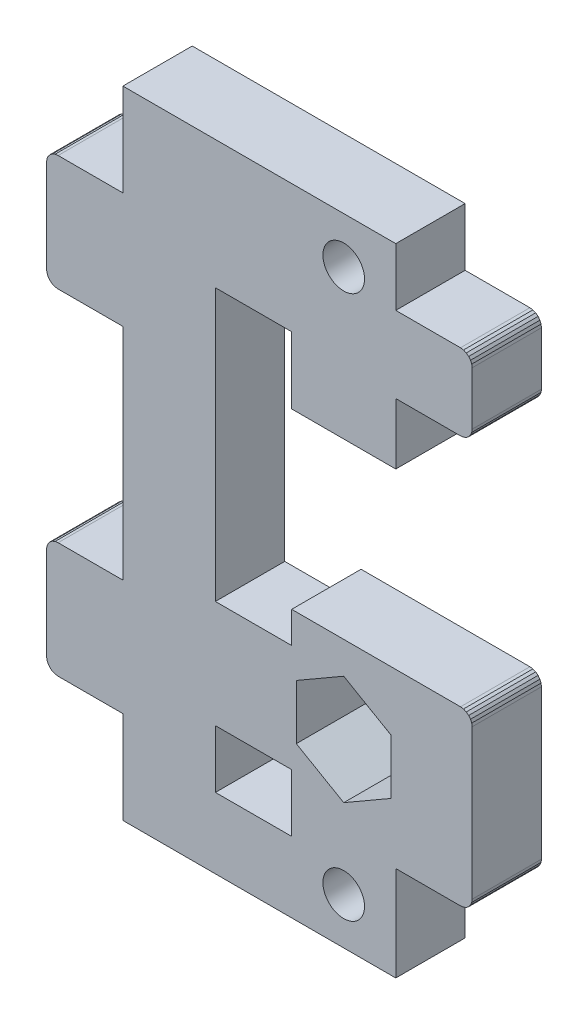
SolidWorks part; units mm, degrees
ref_plane "Plano frontal" through (0, 0, 0) normal (0, 0, 1) x (1, 0, 0)
ref_plane "Plano superior" through (0, 0, 0) normal (0, 1, 0) x (1, 0, 0)
ref_plane "Plano direito" through (0, 0, 0) normal (1, 0, 0) x (0, 0, -1)
sketch "Model" plane through (0, 0, 0) normal (0, 0, 1) x (1, 0, 0)
  line L0 (65.7238, 35.0744) -> (65.6239, 35.3156)
  line L1 (65.6239, 35.3156) -> (65.4649, 35.5227)
  line L2 (65.7578, 34.8156) -> (65.7238, 35.0744)
  line L3 (65.4649, 35.5227) -> (65.2578, 35.6816)
  line L4 (29.4578, 30.5694) -> (29.2507, 30.4104)
  line L5 (29.0918, 30.2033) -> (28.9919, 29.9621)
  line L6 (29.9578, 59.7033) -> (29.699, 59.6693)
  line L7 (29.9578, 20.7033) -> (35.5578, 20.7033)
  line L8 (29.9578, 20.7033) -> (29.699, 20.7374)
  line L9 (65.2578, 62.5694) -> (65.4649, 62.4104)
  line L10 (59.1578, 12.7033) -> (35.5578, 12.7033)
  line L11 (64.7578, 35.8156) -> (50.1578, 35.8156)
  line L12 (28.9919, 29.9621) -> (28.9578, 29.7033)
  line L13 (65.7238, 56.8445) -> (65.7578, 57.1033)
  line L14 (43.5578, 23.8033) -> (43.5618, 18.8033)
  line L15 (50.1578, 56.6033) -> (50.1578, 50.8208)
  line L16 (29.9578, 59.7033) -> (35.5578, 59.7033)
  line L17 (29.699, 30.6693) -> (29.4578, 30.5694)
  line L18 (28.9919, 21.4445) -> (28.9578, 21.7033)
  line L19 (65.0166, 62.6693) -> (65.2578, 62.5694)
  line L20 (29.4578, 59.5694) -> (29.2507, 59.4104)
  line L21 (29.4578, 49.8373) -> (29.699, 49.7374)
  line L22 (35.5578, 49.7033) -> (35.5578, 30.7033)
  line L23 (43.5578, 33.1033) -> (43.5578, 56.6033)
  line L24 (29.699, 59.6693) -> (29.4578, 59.5694)
  line L25 (28.9578, 21.7033) -> (28.9578, 29.7033)
  line L26 (64.7578, 56.1033) -> (65.0166, 56.1374)
  line L27 (65.6239, 62.2033) -> (65.7238, 61.9621)
  line L28 (65.4649, 21.1962) -> (65.6239, 21.4033)
  line L29 (29.2507, 49.9962) -> (29.4578, 49.8373)
  line L30 (65.0166, 35.7815) -> (64.7578, 35.8156)
  line L31 (65.4649, 62.4104) -> (65.6239, 62.2033)
  line L32 (64.7578, 62.7033) -> (59.1578, 62.7033)
  line L33 (65.7238, 21.6445) -> (65.7578, 21.9033)
  line L34 (29.9578, 49.7033) -> (35.5578, 49.7033)
  line L35 (59.1578, 20.9033) -> (59.1578, 12.7033)
  line L36 (28.9578, 50.7033) -> (28.9578, 58.7033)
  line L37 (65.6239, 56.6033) -> (65.7238, 56.8445)
  line L38 (65.4649, 56.3962) -> (65.6239, 56.6033)
  line L39 (29.0918, 50.2033) -> (29.2507, 49.9962)
  line L40 (65.2578, 21.0373) -> (65.4649, 21.1962)
  line L41 (35.5578, 67.7033) -> (35.5578, 59.7033)
  line L42 (28.9578, 50.7033) -> (28.9919, 50.4445)
  line L43 (29.699, 20.7374) -> (29.4578, 20.8373)
  line L44 (50.1578, 23.8085) -> (43.5578, 23.8033)
  line L45 (65.2578, 35.6816) -> (65.0166, 35.7815)
  line L46 (29.9578, 30.7033) -> (29.699, 30.6693)
  line L47 (59.1578, 20.9033) -> (64.7578, 20.9033)
  line L48 (65.7578, 34.8156) -> (65.7578, 21.9033)
  line L49 (65.6239, 21.4033) -> (65.7238, 21.6445)
  line L50 (65.2578, 56.2373) -> (65.4649, 56.3962)
  line L51 (35.5578, 67.7033) -> (59.1578, 67.7033)
  line L52 (65.0166, 56.1374) -> (65.2578, 56.2373)
  line L53 (43.5578, 56.6033) -> (50.1578, 56.6033)
  line L54 (29.2507, 20.9962) -> (29.0918, 21.2033)
  line L55 (29.699, 49.7374) -> (29.9578, 49.7033)
  line L56 (59.1578, 56.1033) -> (59.1578, 50.8208)
  line L57 (28.9919, 58.9621) -> (28.9578, 58.7033)
  line L58 (43.5618, 18.8033) -> (50.1618, 18.8085)
  line L59 (29.0918, 21.2033) -> (28.9919, 21.4445)
  line L60 (29.2507, 59.4104) -> (29.0918, 59.2033)
  line L61 (29.0918, 59.2033) -> (28.9919, 58.9621)
  line L62 (29.2507, 30.4104) -> (29.0918, 30.2033)
  line L63 (35.5578, 30.7033) -> (29.9578, 30.7033)
  line L64 (50.1578, 33.1033) -> (43.5578, 33.1033)
  line L65 (64.7578, 20.9033) -> (65.0166, 20.9374)
  line L66 (59.1578, 62.7033) -> (59.1578, 67.7033)
  line L67 (65.0166, 20.9374) -> (65.2578, 21.0373)
  line L68 (50.1618, 18.8085) -> (50.1578, 23.8085)
  line L69 (50.1578, 35.8156) -> (50.1578, 33.1033)
  line L70 (59.1578, 50.8208) -> (50.1578, 50.8208)
  line L71 (64.7578, 56.1033) -> (59.1578, 56.1033)
  line L72 (65.7578, 61.7033) -> (65.7578, 57.1033)
  line L73 (65.7238, 61.9621) -> (65.7578, 61.7033)
  line L74 (64.7578, 62.7033) -> (65.0166, 62.6693)
  line L75 (28.9919, 50.4445) -> (29.0918, 50.2033)
  line L76 (29.4578, 20.8373) -> (29.2507, 20.9962)
  line L77 (35.5578, 20.7033) -> (35.5578, 12.7033)
  line L78 (50.5578, 30.6879) -> (50.5578, 25.9537)
  line L79 (50.5578, 25.9537) -> (54.6578, 23.5865)
  line L80 (54.6578, 23.5865) -> (58.7578, 25.9537)
  line L81 (58.7578, 25.9537) -> (58.7578, 30.6879)
  line L82 (58.7578, 30.6879) -> (54.6578, 33.0551)
  line L83 (54.6578, 33.0551) -> (50.5578, 30.6879)
  circle A0 centre (54.6578, 63.7033) radius 1.8
  circle A1 centre (54.6578, 16.7033) radius 1.8
extrude "Ressalto-extrusão1" add sketch "Model" along normal blind 6
ref_plane "Plano1" through (0, 0, 3) normal (0, 0, 1) x (1, 0, 0)
ref_plane "Plano2" through (0, 41.8033, 0) normal (0, -1, 0) x (-1, 0, 0)
ref_plane "Plano3" through (0, 40.2033, 0) normal (0, -1, 0) x (-1, 0, 0)
ref_plane "Plano4" through (-0.0148, 37.6862, 0) normal (-0.0004, 1, 0) x (1, 0.0004, 0)
ref_plane "Plano5" through (46.8672, 0.0184, 0) normal (1, 0.0004, 0) x (0, 0, -1)
